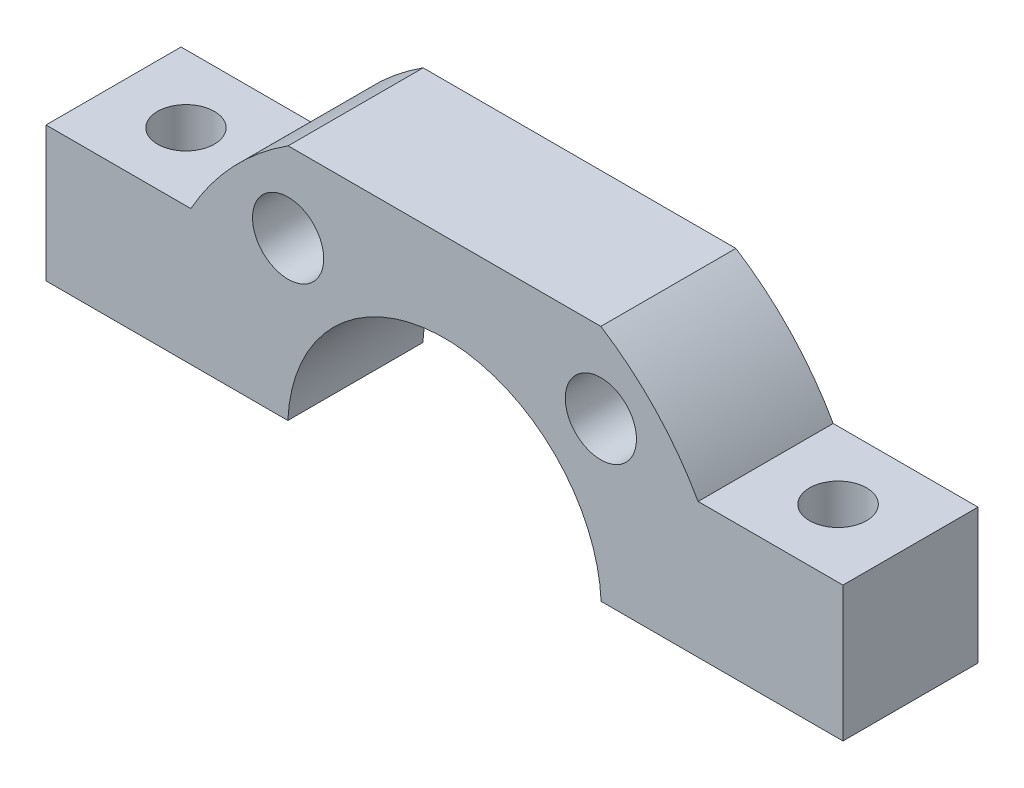
SolidWorks part; units mm, degrees
material "Plain Carbon Steel"
ref_plane "Front Plane" through (0, 0, 0) normal (0, 0, 1) x (1, 0, 0)
ref_plane "Top Plane" through (0, 0, 0) normal (0, 1, 0) x (1, 0, 0)
ref_plane "Right Plane" through (0, 0, 0) normal (1, 0, 0) x (0, 0, -1)
sketch "Sketch1" plane through (0, 0, 0) normal (0, 0, 1) x (1, 0, 0)
  line L0 (-11.03, 0) -> (-28.03, 0)
  line L1 (-28.03, 0) -> (-28.03, 10)
  line L2 (-28.03, 10) -> (-17.8429, 10)
  line L3 (11.03, 0) -> (28.03, 0)
  line L4 (28.03, 0) -> (28.03, 10)
  line L5 (28.03, 10) -> (17.8429, 10)
  line L6 (-11, 17.2444) -> (11, 17.2444)
  arc A0 (11.03, 0) -> (-11.03, 0) centre (0, 0) ccw
  arc A1 (-17.8429, 10) -> (-11, 17.2444) centre (0, 0) cw
  arc A2 (12.49, 10) -> (-12.49, 10) centre (0, 0) ccw construction
  circle A3 centre (11, 11.619) radius 2.505
  circle A4 centre (-11, 11.619) radius 2.505
  arc A6 (11, 17.2444) -> (17.8429, 10) centre (0, 0) cw
  dimension "D1" = 11.03
  dimension "D6" = 20.4541
  dimension "D7" = 16
  dimension "D8" = 5.01
  dimension "D9" = 5.01
  dimension "D2" = 17
  dimension "D3" = 17
  dimension "D4" = 10
  dimension "D5" = 10
extrude "Boss-Extrude2" add sketch "Sketch1" along normal blind 9.5
sketch "Sketch2" plane through (0, 10, 0) normal (0, 1, 0) x (1, 0, 0)
  line L0 (28.03, -9.5) -> (28.03, 0) construction
  line L1 (-28.03, -4.75) -> (28.03, -4.75) construction
  line L2 (-28.03, -9.5) -> (-28.03, 0) construction
  line L3 (-22.9364, 0) -> (-22.9364, -9.5) construction
  line L4 (-17.8429, 0) -> (-28.03, 0) construction
  line L5 (-17.8429, -9.5) -> (-28.03, -9.5) construction
  line L6 (22.9364, 0) -> (22.9364, -9.5) construction
  line L7 (28.03, 0) -> (17.8429, 0) construction
  line L8 (28.03, -9.5) -> (17.8429, -9.5) construction
  circle A0 centre (22.9364, -4.75) radius 2.005
  circle A1 centre (-22.9364, -4.75) radius 2
  dimension "D1" = 4.01
  dimension "D2" = 4
extrude "Cut-Extrude1" cut sketch "Sketch2" against normal up to next
sketch "Sketch3" plane through (0, 0, 0) normal (0, -1, 0) x (1, 0, 0)
  line L1 (-35.1968, 10.8816) -> (37.799, 10.8816)
  line L2 (-35.1968, 10.8816) -> (-35.1968, -7.2673)
  line L3 (-35.1968, -7.2673) -> (37.799, -7.2673)
  line L4 (37.799, 10.8816) -> (37.799, -7.2673)
extrude "Cut-Extrude2" cut sketch "Sketch3" against normal blind 0.5
